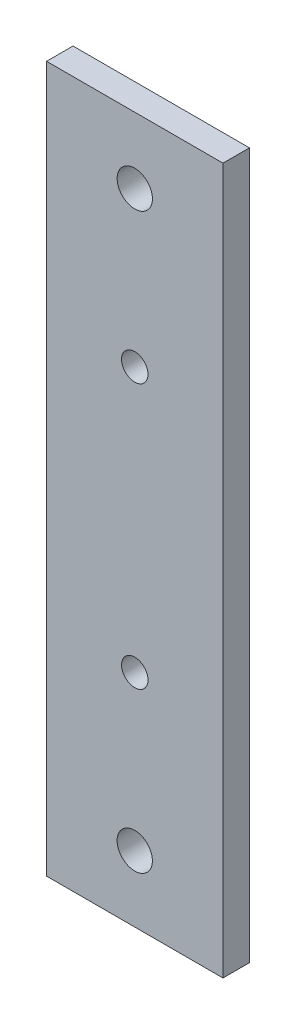
SolidWorks part; units mm, degrees
ref_plane "Plan de face" through (0, 0, 0) normal (0, 0, 1) x (1, 0, 0)
ref_plane "Plan de dessus" through (0, 0, 0) normal (0, 1, 0) x (1, 0, 0)
ref_plane "Plan de droite" through (0, 0, 0) normal (1, 0, 0) x (0, 0, -1)
sketch "Esquisse1" plane through (0, 0, 0) normal (0, 0, 1) x (1, 0, 0)
  line L0 (0, 40) -> (20, 40) construction
  line L1 (0, 0) -> (20, 0)
  line L2 (0, 0) -> (0, 80)
  line L3 (0, 80) -> (20, 80)
  line L4 (20, 0) -> (20, 80)
  line L5 (10, 0) -> (10, 80) construction
  circle A0 centre (10, 55) radius 1.5
  circle A1 centre (10, 25) radius 1.5
  circle A2 centre (10, 72.5) radius 2
  circle A3 centre (10, 7.5) radius 2
  dimension "D3" = 3
  dimension "D6" = 32.5
  dimension "D7" = 4
  dimension "D1" = 20
  dimension "D2" = 80
  dimension "D4" = 15
  dimension "D5" = 10
extrude "Boss.-Extru.1" add sketch "Esquisse1" along normal blind 3
